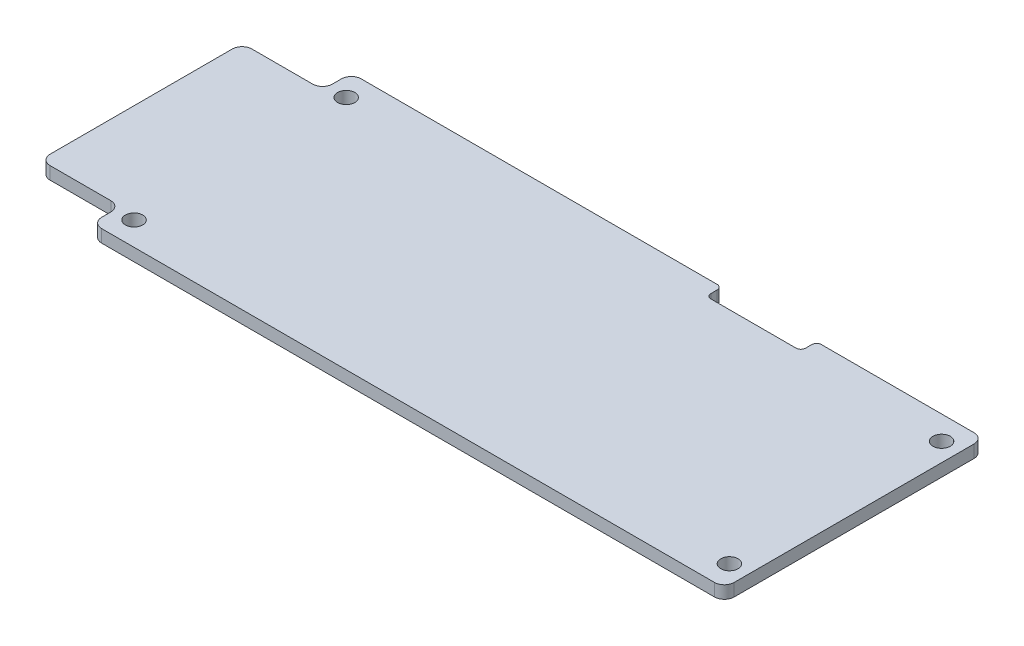
SolidWorks part; units mm, degrees
ref_plane "前视基准面" through (0, 0, 0) normal (0, 0, 1) x (1, 0, 0)
ref_plane "上视基准面" through (0, 0, 0) normal (0, 1, 0) x (1, 0, 0)
ref_plane "右视基准面" through (0, 0, 0) normal (1, 0, 0) x (0, 0, -1)
sketch "草图1" plane through (0, 0, 0) normal (0, 1, 0) x (1, 0, 0)
  line L0 (40.1, 32.9) -> (40.1, 0) construction
  line L1 (1.25, 0) -> (78.95, 0)
  line L2 (0, 1.25) -> (0, 2.4)
  line L3 (1.25, 32.9) -> (46.4, 32.9)
  line L4 (80.2, 1.25) -> (80.2, 31.65)
  line L5 (-9.1211, 16.45) -> (80.2, 16.45) construction
  line L6 (1.25, 29.9) -> (1.25, 32.3962) construction
  line L7 (-1.25, 3.65) -> (-8.95, 3.65)
  line L8 (-10.2, 4.9) -> (-10.2, 28)
  line L9 (-8.95, 29.25) -> (-1.25, 29.25)
  line L10 (0, 30.5) -> (0, 31.65)
  line L14 (59.6, 32.9) -> (78.95, 32.9)
  line L15 (47, 32.3) -> (47, 31.5)
  line L16 (47.6, 30.9) -> (58.4, 30.9)
  line L17 (59, 31.5) -> (59, 32.3)
  circle A0 centre (2.35, 29.9) radius 1.1
  circle A1 centre (77.85, 29.9) radius 1.1
  circle A2 centre (77.85, 3) radius 1.1
  circle A3 centre (2.35, 3) radius 1.1
  arc A4 (80.2, 1.25) -> (78.95, 0) centre (78.95, 1.25) cw
  arc A5 (78.95, 32.9) -> (80.2, 31.65) centre (78.95, 31.65) cw
  arc A6 (0, 1.25) -> (1.25, 0) centre (1.25, 1.25) ccw
  arc A7 (-1.25, 3.65) -> (0, 2.4) centre (-1.25, 2.4) cw
  arc A8 (-10.2, 4.9) -> (-8.95, 3.65) centre (-8.95, 4.9) ccw
  arc A9 (-8.95, 29.25) -> (-10.2, 28) centre (-8.95, 28) ccw
  arc A10 (0, 30.5) -> (-1.25, 29.25) centre (-1.25, 30.5) cw
  arc A11 (0, 31.65) -> (1.25, 32.9) centre (1.25, 31.65) cw
  arc A16 (59, 32.3) -> (59.6, 32.9) centre (59.6, 32.3) cw
  arc A17 (59, 31.5) -> (58.4, 30.9) centre (58.4, 31.5) cw
  arc A18 (47.6, 30.9) -> (47, 31.5) centre (47.6, 31.5) cw
  arc A19 (46.4, 32.9) -> (47, 32.3) centre (46.4, 32.3) cw
  point P25 (80.2, 0)
  point P28 (80.2, 32.9)
  point P31 (0, 0)
  point P34 (0, 3.65)
  point P37 (-10.2, 3.65)
  point P40 (-10.2, 29.25)
  point P43 (0, 29.25)
  point P46 (0, 32.9)
  point P54 (59, 30.9)
  point P57 (47, 30.9)
  point P60 (47, 32.9)
  dimension "D1" = 2.2
  dimension "D2" = 3
  dimension "D3" = 2.35
  dimension "D9" = 1.25
  dimension "D14" = 0.6
  dimension "D4" = 1.25
  dimension "D5" = 32.9
  dimension "D6" = 80.2
  dimension "D7" = 25.6
  dimension "D8" = 10.2
  dimension "D10" = 90.4
  dimension "D11" = 12
  dimension "D12" = 2
  dimension "D13" = 47
extrude "凸台-拉伸1" add sketch "草图1" along normal blind 1.6 contours L8 A9 L9 A10 L10 A11 L3 A5 L4 A4 L1 A6 L2 A7 L7 A8
